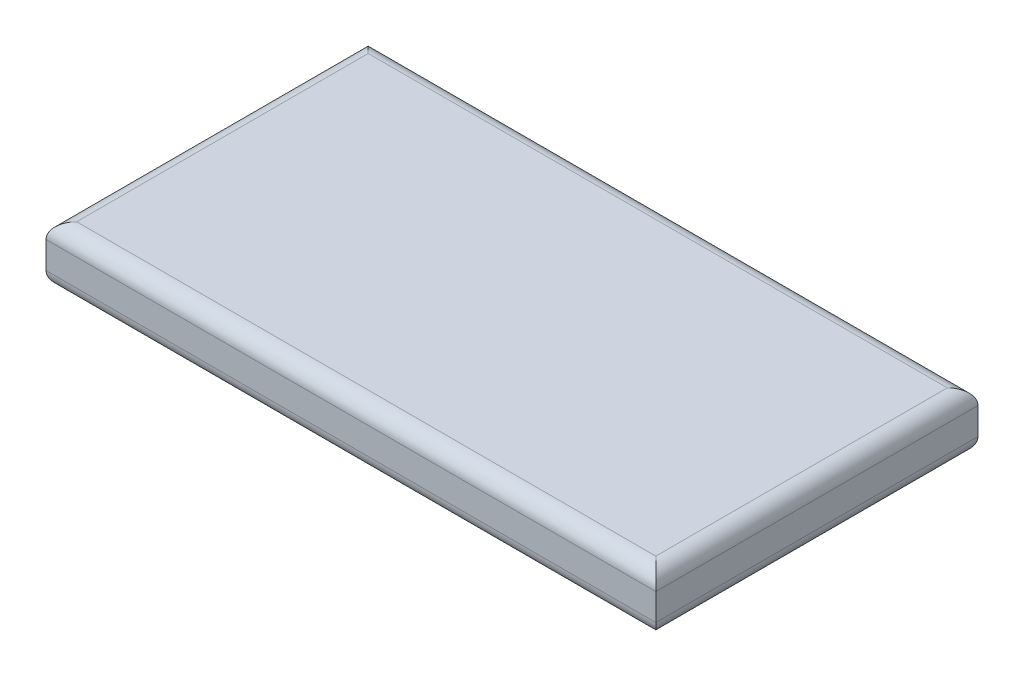
SolidWorks part; units mm, degrees
ref_plane "Front Plane" through (0, 0, 0) normal (0, 0, 1) x (1, 0, 0)
ref_plane "Top Plane" through (0, 0, 0) normal (0, 1, 0) x (1, 0, 0)
ref_plane "Right Plane" through (0, 0, 0) normal (1, 0, 0) x (0, 0, -1)
sketch "Sketch1" plane through (0, 0, 0) normal (0, 1, 0) x (1, 0, 0)
  line L1 (-79.5, 42) -> (79.5, 42)
  line L2 (-79.5, 42) -> (-79.5, -42)
  line L3 (-79.5, -42) -> (79.5, -42)
  line L4 (79.5, 42) -> (79.5, -42)
  line L5 (-79.5, 42) -> (79.5, -42) construction
  line L6 (-79.5, -42) -> (79.5, 42) construction
  point P0 (0, 0)
  dimension "D1" = 159
  dimension "D2" = 84
extrude "Boss-Extrude1" add sketch "Sketch1" along normal blind 15
fillet "Fillet1" radius 4 8 edges at (0, 15, 42) (-79.5, 15, 0) (0, 15, -42) (79.5, 15, 0) (0, 0, -42) (-79.5, 0, 0) (0, 0, 42) (79.5, 0, 0)
